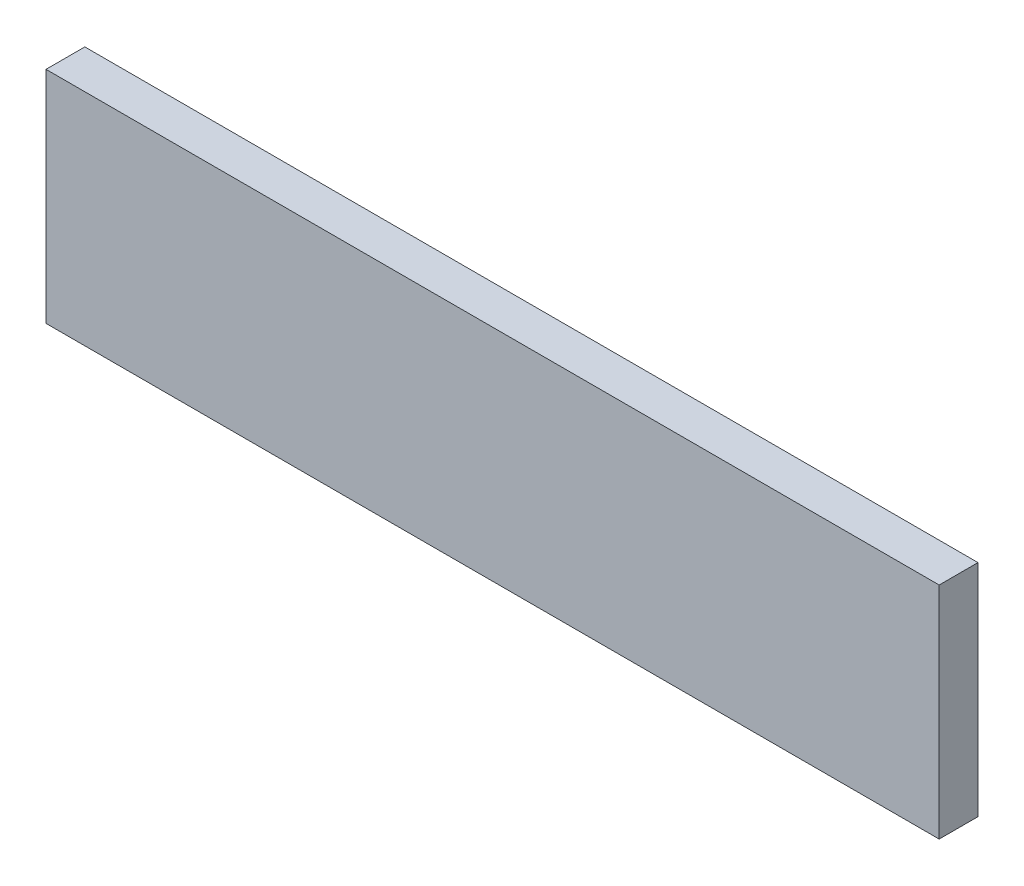
SolidWorks part; units mm, degrees
material "Oak"
ref_plane "Front Plane" through (0, 0, 0) normal (0, 0, 1) x (1, 0, 0)
ref_plane "Top Plane" through (0, 0, 0) normal (0, 1, 0) x (1, 0, 0)
ref_plane "Right Plane" through (0, 0, 0) normal (1, 0, 0) x (0, 0, -1)
sketch "Sketch1" plane through (0, 0, 0) normal (0, 0, 1) x (1, 0, 0)
  line L1 (0, 0) -> (438.15, 0)
  line L2 (0, 0) -> (0, 107.95)
  line L3 (0, 107.95) -> (438.15, 107.95)
  line L4 (438.15, 0) -> (438.15, 107.95)
  dimension "D1" = 438.15
  dimension "D2" = 107.95
extrude "Boss-Extrude1" add sketch "Sketch1" along normal blind 19.05
